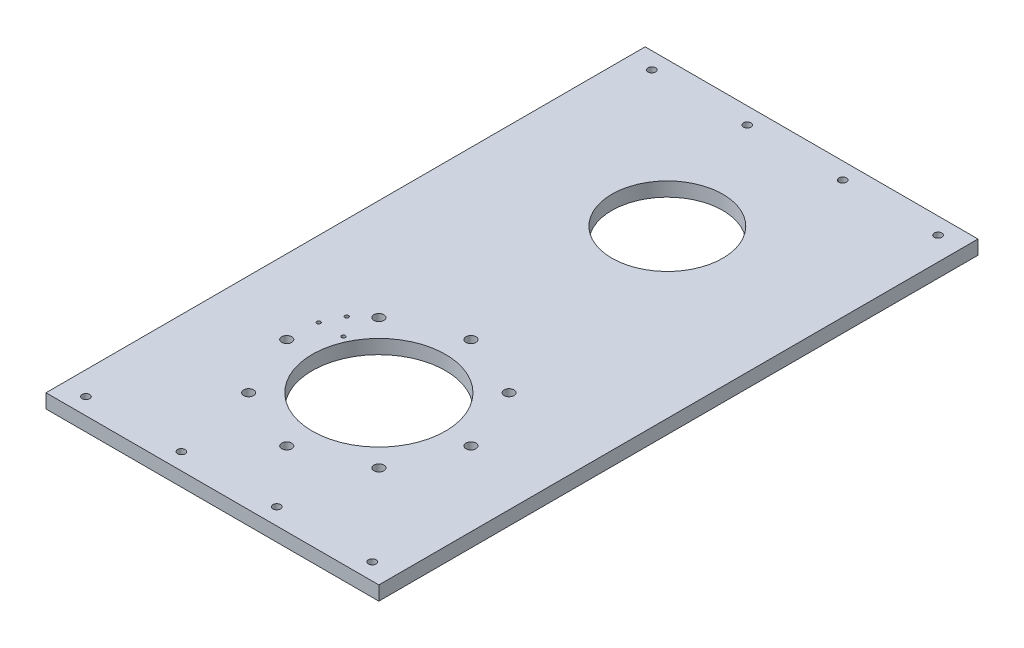
SolidWorks part; units mm, degrees
ref_plane "Front Plane" through (0, 0, 0) normal (0, 0, 1) x (1, 0, 0)
ref_plane "Top Plane" through (0, 0, 0) normal (0, 1, 0) x (1, 0, 0)
ref_plane "Right Plane" through (0, 0, 0) normal (1, 0, 0) x (0, 0, -1)
sketch "Sketch1" plane through (0, 0, 0) normal (0, 1, 0) x (1, 0, 0)
  line L1 (-75, -135) -> (75, -135)
  line L2 (-75, -135) -> (-75, 135)
  line L3 (-75, 135) -> (75, 135)
  line L4 (75, -135) -> (75, 135)
  line L5 (0, 135) -> (0, -135) construction
  line L6 (-75, 0) -> (22.3692, 0) construction
  line L9 (63.727, 0) -> (75, 0) construction
  point P0 (0, 0)
  dimension "D1" = 270
  dimension "D2" = 150
extrude "Boss-Extrude1" add sketch "Sketch1" along normal blind 6.35
sketch "Sketch2" plane through (0, 6.35, 0) normal (0, 1, 0) x (1, 0, 0)
  line L0 (-75, -135) -> (75, -135) construction
  line L1 (0, 135) -> (0, -135) construction
  line L2 (75, 135) -> (-75, 135) construction
  circle A0 centre (0, -60) radius 41.5 construction
  circle A1 centre (0, -18.5) radius 2.25
  circle A2 centre (29.3449, -30.6551) radius 2.25
  circle A3 centre (41.5, -60) radius 2.25
  circle A4 centre (29.3449, -89.3449) radius 2.25
  circle A5 centre (0, -101.5) radius 2.25
  circle A6 centre (-29.3449, -89.3449) radius 2.25
  circle A7 centre (-41.5, -60) radius 2.25
  circle A8 centre (-29.3449, -30.6551) radius 2.25
  circle A9 centre (0, -60) radius 80 construction
  circle A10 centre (0, -60) radius 30
  point P22 (0, -60)
  dimension "D1" = 83
  dimension "D2" = 4.5
  dimension "D4" = 160
  dimension "D6" = 60
  dimension "D5" = 75
  dimension "D3" = 8
extrude "Cut-Extrude1" cut sketch "Sketch2" against normal through all
sketch "Sketch6" plane through (0, 6.35, 0) normal (0, 1, 0) x (1, 0, 0)
  line L0 (0, -60) -> (-38.9712, -41.8274) construction
  line L1 (0, -60) -> (0, -18.5) construction
  line L2 (-40.9787, -46.1324) -> (-36.9638, -37.5225) construction
  line L3 (-36.9638, -37.5225) -> (-27.9007, -41.7486) construction
  circle A0 centre (0, -60) radius 30 construction
  circle A1 centre (-36.9638, -37.5225) radius 0.85
  circle A2 centre (-40.9787, -46.1324) radius 0.85
  circle A5 centre (-29.9082, -46.0536) radius 0.85
  point P7 (-38.9712, -41.8274)
  dimension "D4" = 1.7
  dimension "D5" = 10
  dimension "D7" = 10
  dimension "D6" = 1.7
  dimension "D1" = 43
  dimension "D2" = 9.5
  dimension "D3" = 65
extrude "Cut-Extrude5" cut sketch "Sketch6" against normal through all
sketch "Sketch7" plane through (0, 6.35, 0) normal (0, 1, 0) x (1, 0, 0)
  line L0 (-75, 0) -> (75, 0) construction
  line L1 (-75, 135) -> (-75, -135) construction
  line L2 (75, -135) -> (75, 135) construction
  line L3 (0, -135) -> (0, 135) construction
  line L4 (-75, -135) -> (75, -135) construction
  line L5 (75, 135) -> (-75, 135) construction
  circle A0 centre (-64.5, -127.5) radius 1.7
  circle A1 centre (-21.5, -127.5) radius 1.7
  circle A2 centre (21.5, -127.5) radius 1.7
  circle A3 centre (64.5, -127.5) radius 1.7
  circle A4 centre (64.5, 127.5) radius 1.7
  circle A5 centre (21.5, 127.5) radius 1.7
  circle A6 centre (-64.5, 127.5) radius 1.7
  circle A7 centre (-21.5, 127.5) radius 1.7
  dimension "D1" = 3.4
  dimension "D2" = 3.4
  dimension "D3" = 7.5
  dimension "D4" = 7.5
  dimension "D5" = 10.5
  dimension "D6" = 43
extrude "Cut-Extrude6" cut sketch "Sketch7" against normal through all
sketch "Sketch8" plane through (0, 6.35, 0) normal (0, 1, 0) x (1, 0, 0)
  line L1 (75, 135) -> (-75, 135) construction
  line L2 (69, -20.6305) -> (69, 135) construction
  line L3 (75, -135) -> (75, 135) construction
  line L5 (49, 41.8036) -> (49, 135) construction
  circle A0 centre (0, 70) radius 25
  circle A1 centre (0, -60) radius 30 construction
  dimension "D1" = 130
  dimension "D2" = 50
  dimension "D3" = 6
  dimension "D4" = 20
extrude "Cut-Extrude9" cut sketch "Sketch8" against normal through all
